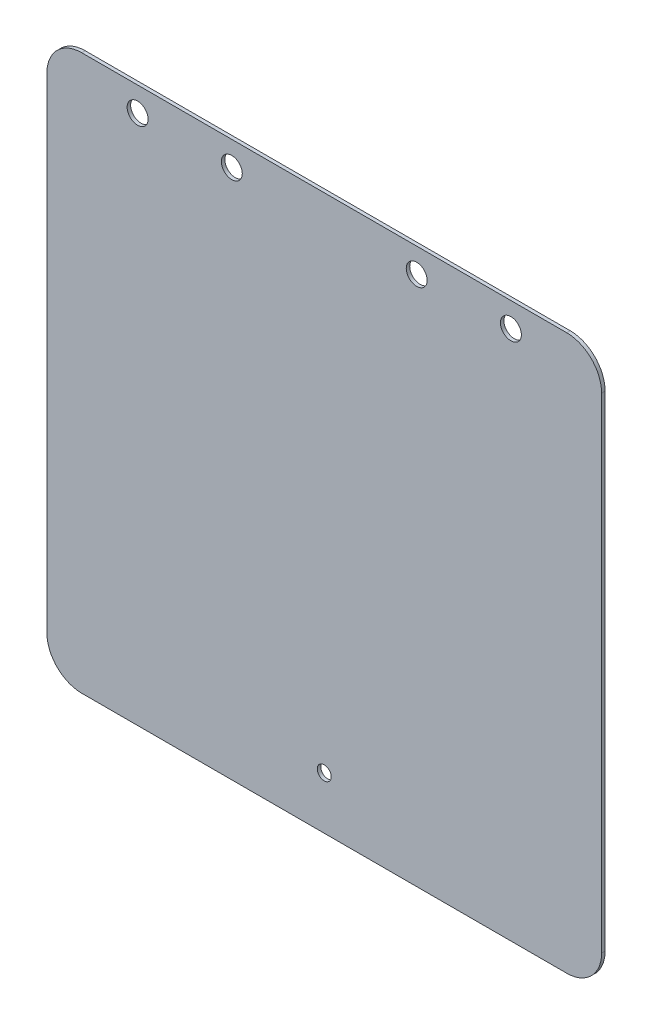
SolidWorks part; units mm, degrees
ref_plane "정면" through (0, 0, 0) normal (0, 0, 1) x (1, 0, 0)
ref_plane "윗면" through (0, 0, 0) normal (0, 1, 0) x (1, 0, 0)
ref_plane "우측면" through (0, 0, 0) normal (1, 0, 0) x (0, 0, -1)
sketch "스케치1" plane through (0, 0, 0) normal (0, 0, 1) x (1, 0, 0)
  line L1 (-69.5, -79.5) -> (69.5, -79.5)
  line L2 (-79.5, -69.5) -> (-79.5, 69.5)
  line L3 (-69.5, 79.5) -> (69.5, 79.5)
  line L4 (79.5, -69.5) -> (79.5, 69.5)
  line L5 (-79.5, -79.5) -> (79.5, 79.5) construction
  line L6 (-79.5, 79.5) -> (79.5, -79.5) construction
  arc A0 (69.5, 79.5) -> (79.5, 69.5) centre (69.5, 69.5) cw
  arc A1 (79.5, -69.5) -> (69.5, -79.5) centre (69.5, -69.5) cw
  arc A2 (-79.5, -69.5) -> (-69.5, -79.5) centre (-69.5, -69.5) ccw
  arc A3 (-79.5, 69.5) -> (-69.5, 79.5) centre (-69.5, 69.5) cw
  point P4 (0, 0)
  dimension "D3" = 10
  dimension "D1" = 159
  dimension "D2" = 159
extrude "보스-돌출1" add sketch "스케치1" along normal blind 1
sketch "스케치2" plane through (0, 0, 1) normal (0, 0, 1) x (1, 0, 0)
  line L0 (69.5, 79.5) -> (-69.5, 79.5) construction
  line L1 (-59.5, 79.5) -> (-20.5, 79.5)
  line L2 (-59.5, 79.5) -> (-59.5, 65.5)
  line L3 (-59.5, 65.5) -> (-20.5, 65.5)
  line L4 (-20.5, 79.5) -> (-20.5, 65.5)
  line L5 (-59.5, 79.5) -> (-20.5, 65.5) construction
  line L6 (-59.5, 65.5) -> (-20.5, 79.5) construction
  line L7 (0, 0) -> (0, 79.5) construction
  line L8 (59.5, 65.5) -> (20.5, 79.5) construction
  line L9 (59.5, 79.5) -> (20.5, 65.5) construction
  line L10 (20.5, 79.5) -> (20.5, 65.5)
  line L11 (59.5, 65.5) -> (20.5, 65.5)
  line L12 (59.5, 79.5) -> (59.5, 65.5)
  line L13 (59.5, 79.5) -> (20.5, 79.5)
  circle A0 centre (-53.5, 72.5) radius 3
  circle A1 centre (-26.5, 72.5) radius 3
  circle A2 centre (26.5, 72.5) radius 3
  circle A3 centre (53.5, 72.5) radius 3
  point P4 (-40, 72.5)
  point P22 (40, 72.5)
  dimension "D1" = 6
  dimension "D2" = 6
  dimension "D3" = 6
  dimension "D4" = 6
  dimension "D5" = 14
  dimension "D6" = 39
  dimension "D7" = 20.5
extrude "컷-돌출1" cut sketch "스케치2" against normal blind 1 contours A0 | A1 | A2 | A3
sketch "스케치3" plane through (0, 0, 1) normal (0, 0, 1) x (1, 0, 0)
  line L0 (-69.5, -79.5) -> (69.5, -79.5) construction
  circle A0 centre (0, -64.5) radius 2
  dimension "D1" = 4
  dimension "D2" = 15
extrude "컷-돌출2" cut sketch "스케치3" against normal blind 1
